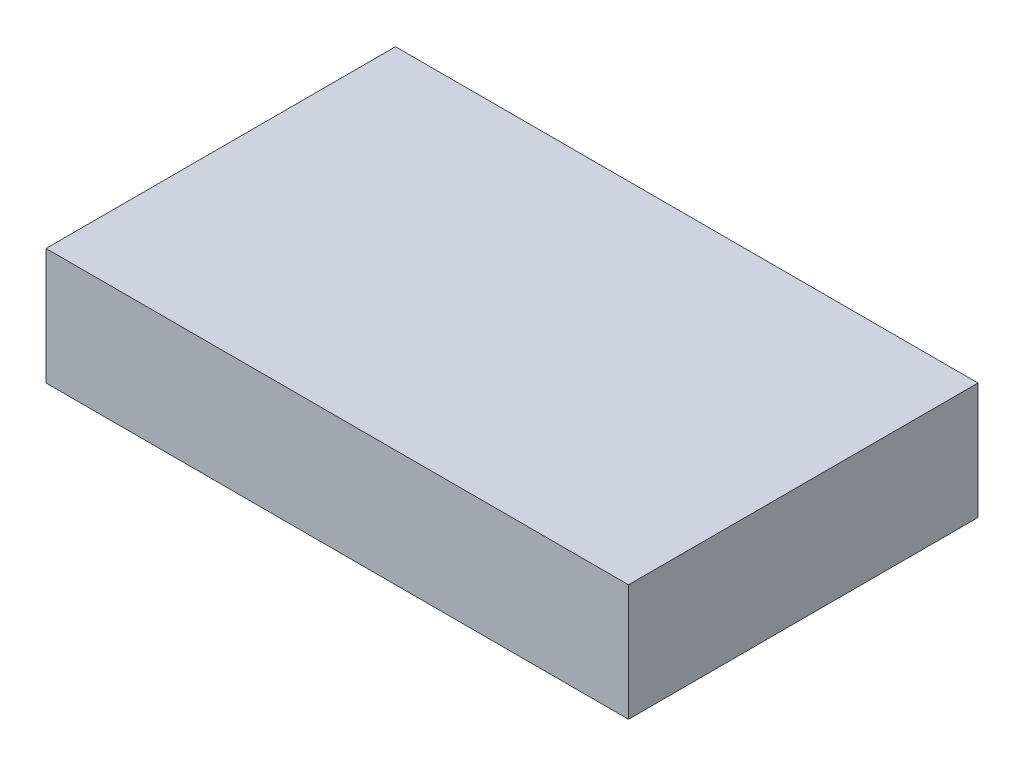
SolidWorks part; units mm, degrees
ref_plane "Front Plane" through (0, 0, 0) normal (0, 0, 1) x (1, 0, 0)
ref_plane "Top Plane" through (0, 0, 0) normal (0, 1, 0) x (1, 0, 0)
ref_plane "Right Plane" through (0, 0, 0) normal (1, 0, 0) x (0, 0, -1)
sketch "Sketch1" plane through (0, 0, 0) normal (0, 0, 1) x (1, 0, 0)
  line L1 (0, 0) -> (95.25, 0)
  line L2 (0, 0) -> (0, 19.05)
  line L3 (0, 19.05) -> (95.25, 19.05)
  line L4 (95.25, 0) -> (95.25, 19.05)
  dimension "D1" = 95.25
  dimension "D2" = 19.05
extrude "Boss-Extrude1" add sketch "Sketch1" along normal blind 57.15
